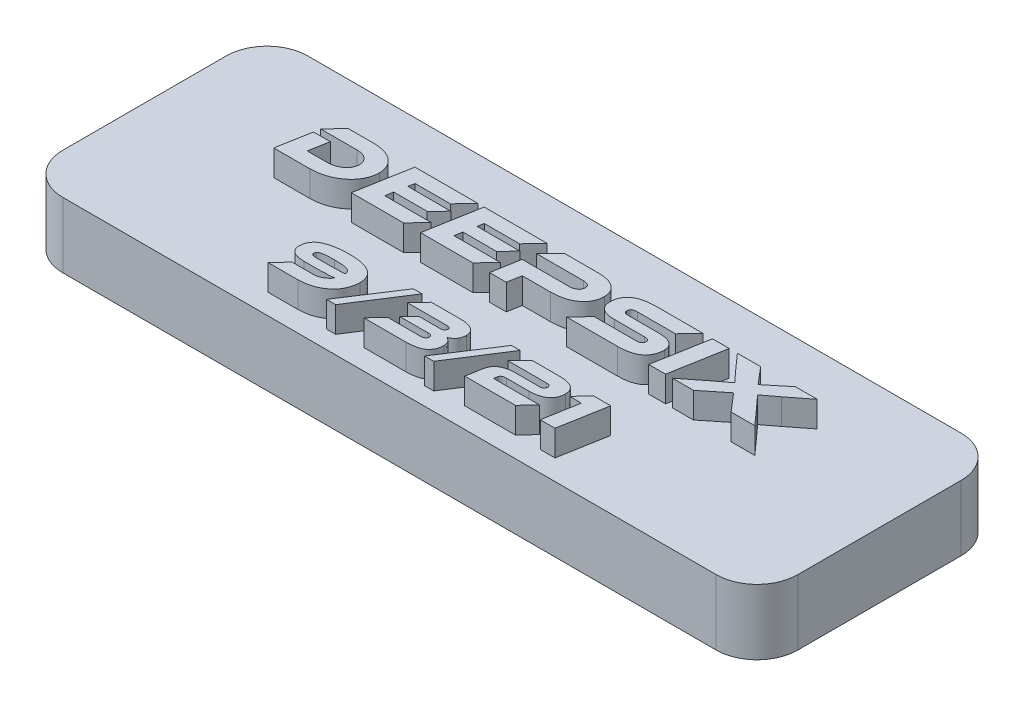
SolidWorks part; units mm, degrees
ref_plane "Front Plane" through (0, 0, 0) normal (0, 0, 1) x (1, 0, 0)
ref_plane "Top Plane" through (0, 0, 0) normal (0, 1, 0) x (1, 0, 0)
ref_plane "Right Plane" through (0, 0, 0) normal (1, 0, 0) x (0, 0, -1)
sketch "Sketch1" plane through (0, 0, 0) normal (0, 1, 0) x (1, 0, 0)
  line L1 (-28.575, 9.525) -> (28.575, 9.525)
  line L2 (-28.575, 9.525) -> (-28.575, -9.525)
  line L3 (-28.575, -9.525) -> (28.575, -9.525)
  line L4 (28.575, 9.525) -> (28.575, -9.525)
  line L5 (-28.575, 9.525) -> (28.575, -9.525) construction
  line L6 (-28.575, -9.525) -> (28.575, 9.525) construction
  point P0 (0, 0)
  dimension "D1" = 57.15
  dimension "D2" = 19.05
extrude "Boss-Extrude1" add sketch "Sketch1" along normal up to surface (5.08 mm away)
fillet "Fillet1" radius 3.175 4 edges at (-28.575, 2.54, 9.525) (-28.575, 2.54, -9.525) (28.575, 2.54, 9.525) (28.575, 2.54, -9.525)
sketch "Sketch3" plane through (0, 5.08, 0) normal (0, 1, 0) x (1, 0, 0)
  line L0 (28.575, -7.9375) -> (-28.575, -7.9375) construction
  line L1 (28.575, -6.35) -> (28.575, 6.35) construction
  line L2 (-28.575, 6.35) -> (-28.575, -6.35) construction
  line L3 (28.575, 0) -> (-28.575, 0) construction
  line L5 (-25.4, -9.525) -> (25.4, -9.525) construction
  line L6 (25.4, 9.525) -> (-25.4, 9.525) construction
  text T0 "DEEPSIX\r\n" font "Ethnocentric Rg" height in points 16
  text T1 "9/3/21" font "Ethnocentric Rg" height in points 14
  point P8 (-28.575, 0)
  dimension "D1" = 1.5875
extrude "Boss-Extrude2" add sketch "Sketch3" along normal blind 2
sketch "Sketch4" plane through (0, 0, 0) normal (0, -1, 0) x (1, 0, 0)
  line L0 (25.4, 0) -> (-25.4, 0) construction
  circle A0 centre (-25.4, 0) radius 0.9
  circle A1 centre (25.4, 0) radius 0.9
  point P3 (0, 0)
  dimension "D2" = 1.8
  dimension "D1" = 50.8
extrude "Cut-Extrude1" cut sketch "Sketch4" against normal blind 4
